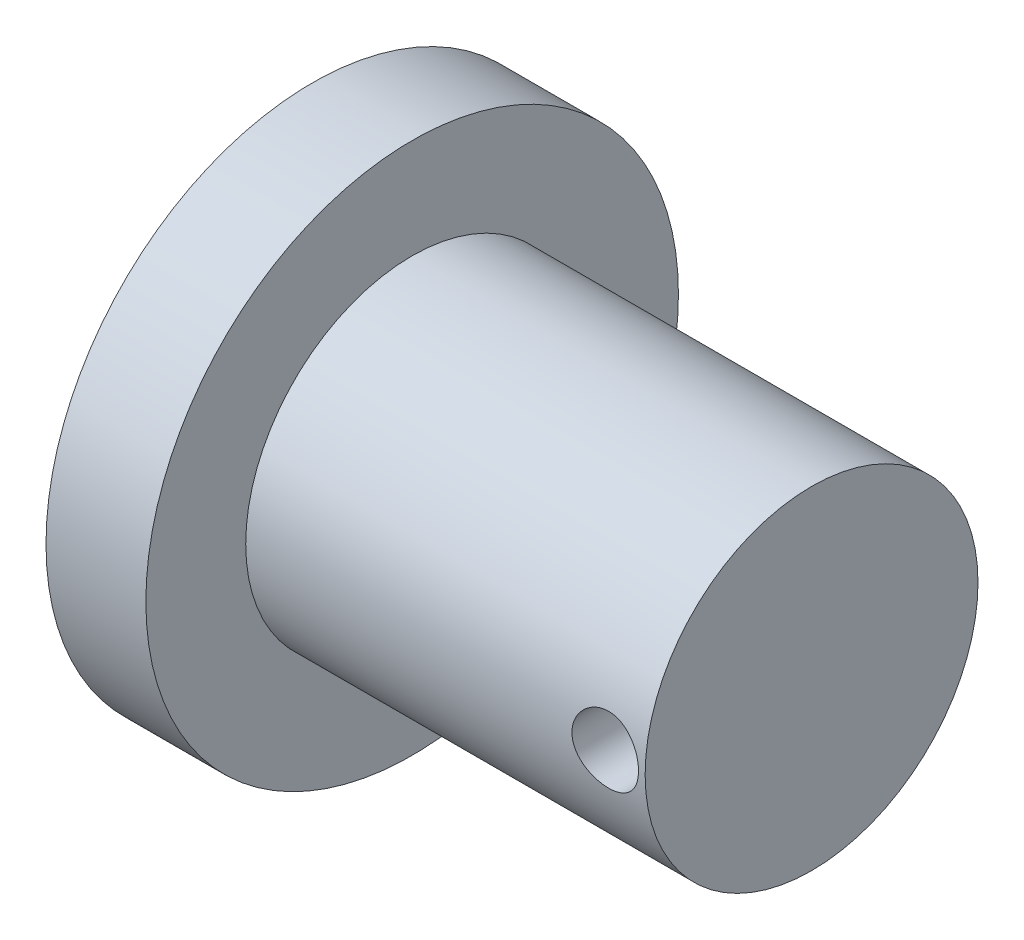
SolidWorks part; units mm, degrees
ref_plane "Front Plane" through (0, 0, 0) normal (0, 0, 1) x (1, 0, 0)
ref_plane "Top Plane" through (0, 0, 0) normal (0, 1, 0) x (1, 0, 0)
ref_plane "Right Plane" through (0, 0, 0) normal (1, 0, 0) x (0, 0, -1)
sketch "Sketch2" plane through (0, 0, 0) normal (0, 0, 1) x (1, 0, 0)
  line L0 (-25.0885, 0) -> (-10.0885, 0)
  line L1 (-10.0885, 0) -> (-10.0885, 5)
  line L2 (-10.0885, 5) -> (-22.0885, 5)
  line L3 (-22.0885, 5) -> (-22.0885, 8)
  line L4 (-22.0885, 8) -> (-25.0885, 8)
  line L5 (-25.0885, 8) -> (-25.0885, 0)
  dimension "D1" = 5
  dimension "D2" = 12
  dimension "D3" = 15
  dimension "D4" = 8
revolve "Revolve1" add sketch "Sketch2" angle 360 about L0
sketch "Sketch3" plane through (0, 0, 0) normal (0, 0, 1) x (1, 0, 0)
  line L0 (-10.0885, -5) -> (-10.0885, 5) construction
  circle A0 centre (-11.2885, 0) radius 1
  dimension "D1" = 1.2
extrude "Cut-Extrude1" cut sketch "Sketch3" against normal through all both and the other way through all
